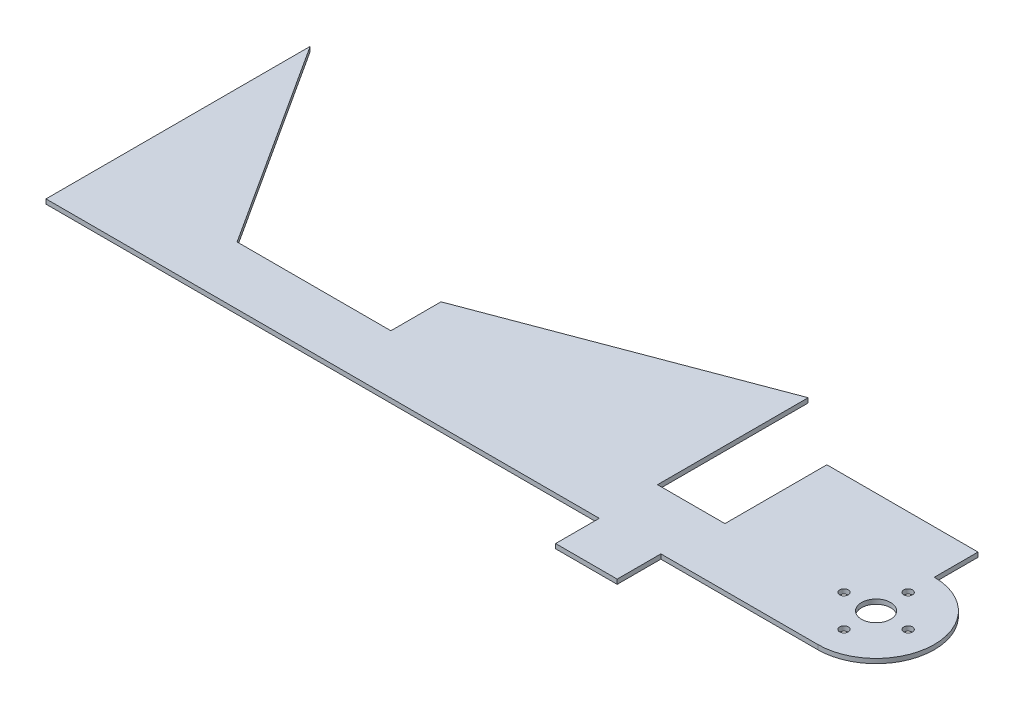
SolidWorks part; units mm, degrees
ref_plane "Front Plane" through (0, 0, 0) normal (0, 0, 1) x (1, 0, 0)
ref_plane "Top Plane" through (0, 0, 0) normal (0, 1, 0) x (1, 0, 0)
ref_plane "Right Plane" through (0, 0, 0) normal (1, 0, 0) x (0, 0, -1)
sketch "Sketch1" plane through (0, 0, 0) normal (0, 1, 0) x (1, 0, 0)
  line L1 (-31.3515, -35.0605) -> (-60.325, 9.8408)
  line L2 (-60.325, 9.8408) -> (-60.325, -47.7605)
  line L3 (-60.325, -47.7605) -> (0, -47.7605)
  line L8 (0, -47.7605) -> (60.325, -47.7605)
  line L9 (60.325, -47.7605) -> (60.325, -2.201)
  line L10 (60.325, -2.201) -> (-26.7915, -35.0605)
  line L12 (-31.3515, -35.0605) -> (-26.7915, -35.0605)
  point P0 (53.975, -4.5961)
  point P13 (-53.975, 0)
  dimension "D1" = 6.35
  dimension "D3" = 32.833
  dimension "D7" = 53.975
  dimension "D2" = 12.7
  dimension "D4" = 44.9013
  dimension "D5" = 32.8595
  dimension "D6" = 6.35
  dimension "D8" = 53.975
  dimension "D9" = 69.334
sketch "Sketch2" plane through (0, 0, 0) normal (0, 1, 0) x (1, 0, 0)
  line L5 (0, -47.7605) -> (60.325, -47.7605)
  line L6 (-31.3515, -35.0605) -> (-60.325, 9.8408)
  line L7 (-60.325, 9.8408) -> (-60.325, -47.7605)
  line L8 (-60.325, -47.7605) -> (0, -47.7605)
  line L11 (-31.3515, -35.0605) -> (-60.325, 9.8408)
  line L12 (-60.325, 9.8408) -> (-60.325, -47.7605)
  line L13 (-60.325, -47.7605) -> (0, -47.7605)
  line L16 (0, -47.7605) -> (60.325, -47.7605)
  line L17 (60.325, -47.7605) -> (60.325, -2.201)
  line L18 (60.325, -47.7605) -> (60.325, -2.201)
  line L19 (60.325, -2.201) -> (-26.7915, -35.0605)
  line L20 (60.325, -2.201) -> (-26.7915, -35.0605)
  line L21 (-26.7915, -35.0605) -> (-31.3515, -35.0605)
  line L22 (-26.7915, -35.0605) -> (-31.3515, -35.0605)
  dimension "D1" = 0
extrude "Boss-Extrude2" add sketch "Sketch2" along normal blind 1
sketch "Sketch3"
  dimension "D5" = 25.4
  dimension "D2" = 14.7
  dimension "D3" = 107.9851
other "AlignGroup1"
sketch "Sketch5" plane through (0, 0, 0) normal (0, 1, 0) x (1, 0, 0)
  line L38 (60.325, -47.7605) -> (75.025, -47.7605) construction
  line L39 (60.325, -47.7605) -> (60.325, -35.0605) construction
  line L40 (60.325, -35.0605) -> (75.025, -35.0605) construction
  line L41 (75.025, -22.3605) -> (75.025, -35.0605) construction
  line L42 (107.9851, -22.3605) -> (75.025, -22.3605) construction
  line L43 (107.9851, -47.7605) -> (75.025, -47.7605) construction
  line L44 (60.325, -47.7605) -> (75.025, -47.7605)
  line L45 (60.325, -47.7605) -> (60.325, -35.0605)
  line L46 (60.325, -35.0605) -> (75.025, -35.0605)
  line L47 (75.025, -22.3605) -> (75.025, -35.0605)
  line L48 (107.9851, -22.3605) -> (75.025, -22.3605)
  line L49 (107.9851, -47.7605) -> (75.025, -47.7605)
  circle A1 centre (107.9851, -35.0605) radius 12.7
  arc A5 (107.9851, -47.7605) -> (107.9851, -22.3605) centre (107.9851, -35.0605) ccw
  dimension "D1" = 0
extrude "Boss-Extrude4" add sketch "Sketch5" along normal blind 1
sketch "Sketch4" plane through (0, 1, 0) normal (0, 1, 0) x (1, 0, 0)
  circle A1 centre (107.9851, -35.0605) radius 3.175
  circle A2 centre (114.9851, -35.0605) radius 0.95
  circle A3 centre (107.9851, -42.0605) radius 0.95
  circle A4 centre (107.9851, -35.0605) radius 3.175
  circle A5 centre (100.9851, -35.0605) radius 0.95
  circle A6 centre (107.9851, -35.0605) radius 3.175
  circle A7 centre (107.9851, -28.0605) radius 0.95
  circle A8 centre (107.9851, -35.0605) radius 3.175
  point P17 (107.9851, -35.0605)
  dimension "D1" = 6.35
  dimension "D3" = 1.9
  dimension "D2" = 7
  dimension "D4" = 4
extrude "Cut-Extrude1" cut sketch "Sketch4" against normal through all both contours A1 | A3 | A7 | A5 | A2
sketch "Sketch6" plane through (0, 1, 0) normal (0, 1, 0) x (1, 0, 0)
  line L0 (75.025, 199981.8306) -> (75.025, -47.7605) construction
  line L9 (73.755, -47.7605) -> (60.325, -47.7605)
  line L10 (73.755, -47.7605) -> (73.755, -57.2855)
  line L11 (73.755, -57.2855) -> (60.325, -57.2855)
  line L12 (60.325, -47.7605) -> (60.325, -57.2855)
  line L13 (60.325, -47.7605) -> (60.325, -35.0605) construction
  line L16 (75.025, -22.3605) -> (107.9851, -22.3605)
  line L17 (75.025, -22.3605) -> (75.025, -12.8355)
  line L18 (75.025, -12.8355) -> (107.9851, -12.8355)
  line L19 (107.9851, -22.3605) -> (107.9851, -12.8355)
  dimension "D1" = 9.525
  dimension "D2" = 1.27
extrude "Boss-Extrude5" add sketch "Sketch6" against normal blind 1
sketch "Sketch8" plane through (0, 1, 0) normal (0, 1, 0) x (1, 0, 0)
  line L0 (-26.7915, -35.0605) -> (2.182, -24.1319)
  line L1 (60.325, -2.201) -> (-26.7915, -35.0605) construction
  line L2 (2.182, -24.1319) -> (2.182, -35.0605)
  line L3 (2.182, -35.0605) -> (-26.7915, -35.0605)
  line L4 (-31.3515, -35.0605) -> (-60.325, -35.0605) construction
  line L5 (-60.325, 9.8408) -> (-60.325, -47.7605) construction
extrude "Cut-Extrude2" cut sketch "Sketch8" against normal through all both
equation "\"D2@Sketch3\"=14.7mm"
equation "\"D2@Sketch4\"=7mm"
equation "\"D3@Sketch4\"=1.9mm"
equation "\"long projected\"= 1.25in"
equation "\"long slope\"= 1"
equation "\"short projected\"= \"long projected\" / 3.75"
equation "\"short slope\"= \"long slope\" * 3.75"
equation "\"long raw\"= \"long projected\" / cos ( atn ( \"long slope\" ) )"
equation "\"short raw\"= \"short projected\" / cos ( atn ( \"short slope\" ) )"
equation "\"short angle\"= atn ( \"short slope\" )"
equation "\"long angle\"= atn(\"long slope\")"
equation "\"servo deflection at release\"= atn ( \"long projected\" / ( 3.672640 + 4.25 / 2 ) )"
equation "\"D3@Sketch1\"=45-\"servo deflection at release\""
equation "\"D4@Sketch1\"=\"long raw\""
equation "\"D5@Sketch1\"=\"short raw\""
equation "\"D3@Sketch3\"=3.672640in+14.7mm"
equation "\"D9@Sketch1\"=45+\"servo deflection at release\"*2"
